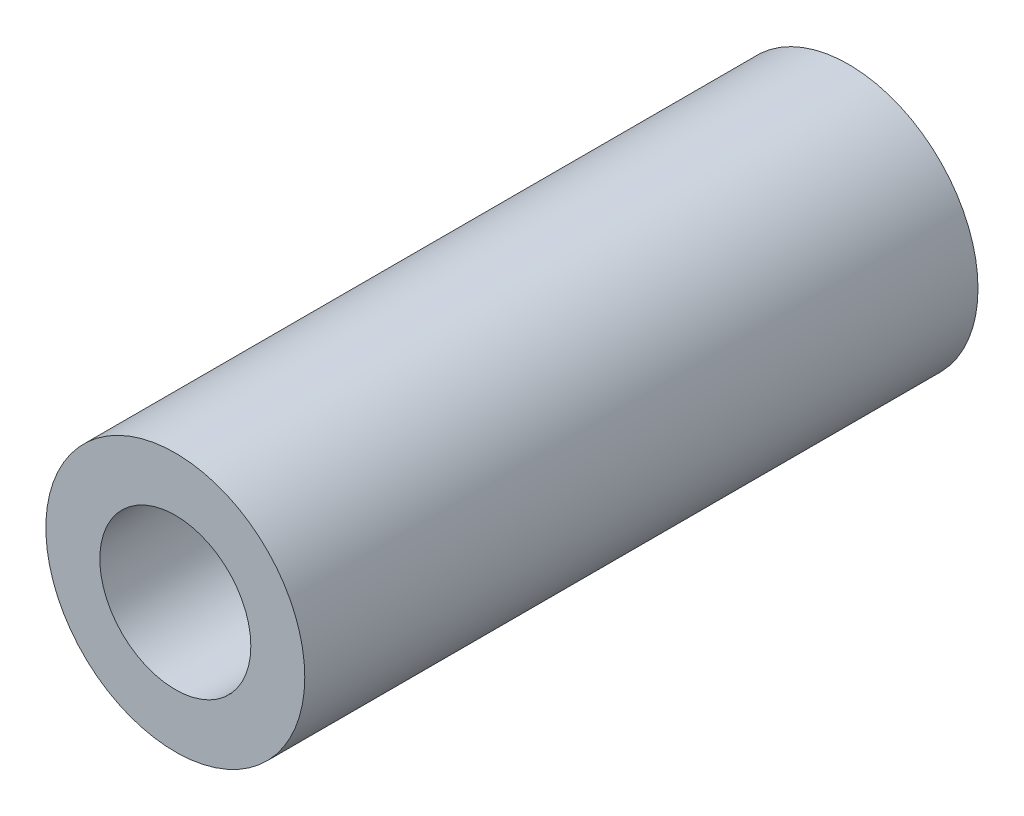
SolidWorks part; units mm, degrees
material "ABS"
ref_plane "前视基准面" through (0, 0, 0) normal (0, 0, 1) x (1, 0, 0)
ref_plane "上视基准面" through (0, 0, 0) normal (0, 1, 0) x (1, 0, 0)
ref_plane "右视基准面" through (0, 0, 0) normal (1, 0, 0) x (0, 0, -1)
sketch "草图1" plane through (0, 0, 0) normal (0, 0, 1) x (1, 0, 0)
  circle A0 centre (0, 0) radius 3.5
  circle A1 centre (0, 0) radius 6
  dimension "D1" = 7
  dimension "D2" = 12
extrude "凸台-拉伸1" add sketch "草图1" along normal mid plane 31.2
